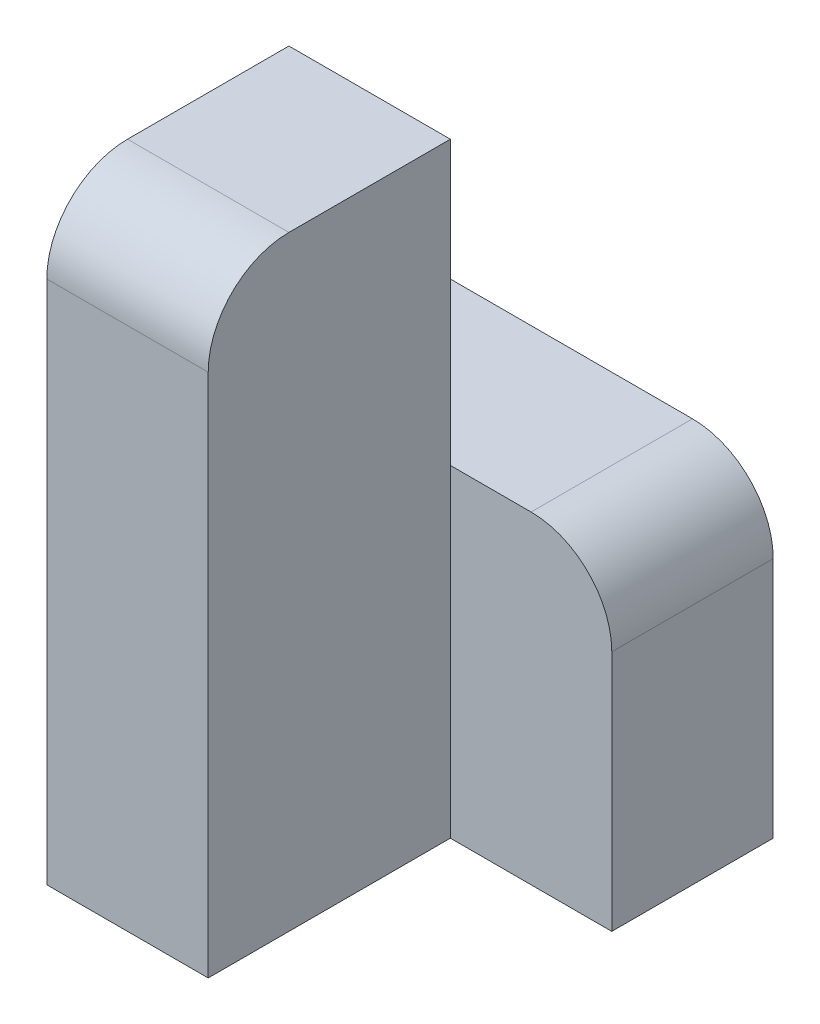
SolidWorks part; units mm, degrees
ref_plane "Front Plane" through (0, 0, 0) normal (0, 0, 1) x (1, 0, 0)
ref_plane "Top Plane" through (0, 0, 0) normal (0, 1, 0) x (1, 0, 0)
ref_plane "Right Plane" through (0, 0, 0) normal (1, 0, 0) x (0, 0, -1)
sketch "Sketch1" plane through (0, 0, 0) normal (0, 0, 1) x (1, 0, 0)
  line L1 (-30, -75) -> (-10, -75)
  line L2 (-10, -75) -> (-10, 0)
  line L3 (-10, 0) -> (-30, 0)
  line L4 (-30, 0) -> (-30, -75)
  dimension "D1" = 20
  dimension "Width" = 75
extrude "Boss-Extrude1" add sketch "Sketch1" along normal blind 30
sketch "Sketch2" plane through (0, 0, 0) normal (0, 0, 1) x (1, 0, 0)
  line L1 (-30, -75) -> (10, -75)
  line L2 (10, -75) -> (10, -35)
  line L3 (10, -35) -> (-30, -35)
  line L4 (-30, -35) -> (-30, -75)
  dimension "D1" = 40
  dimension "Width" = 40
extrude "Boss-Extrude2" add sketch "Sketch2" against normal blind 20
fillet "Fillet1" radius 10 2 edges at (10, -35, -10) (-20, 0, 30)
